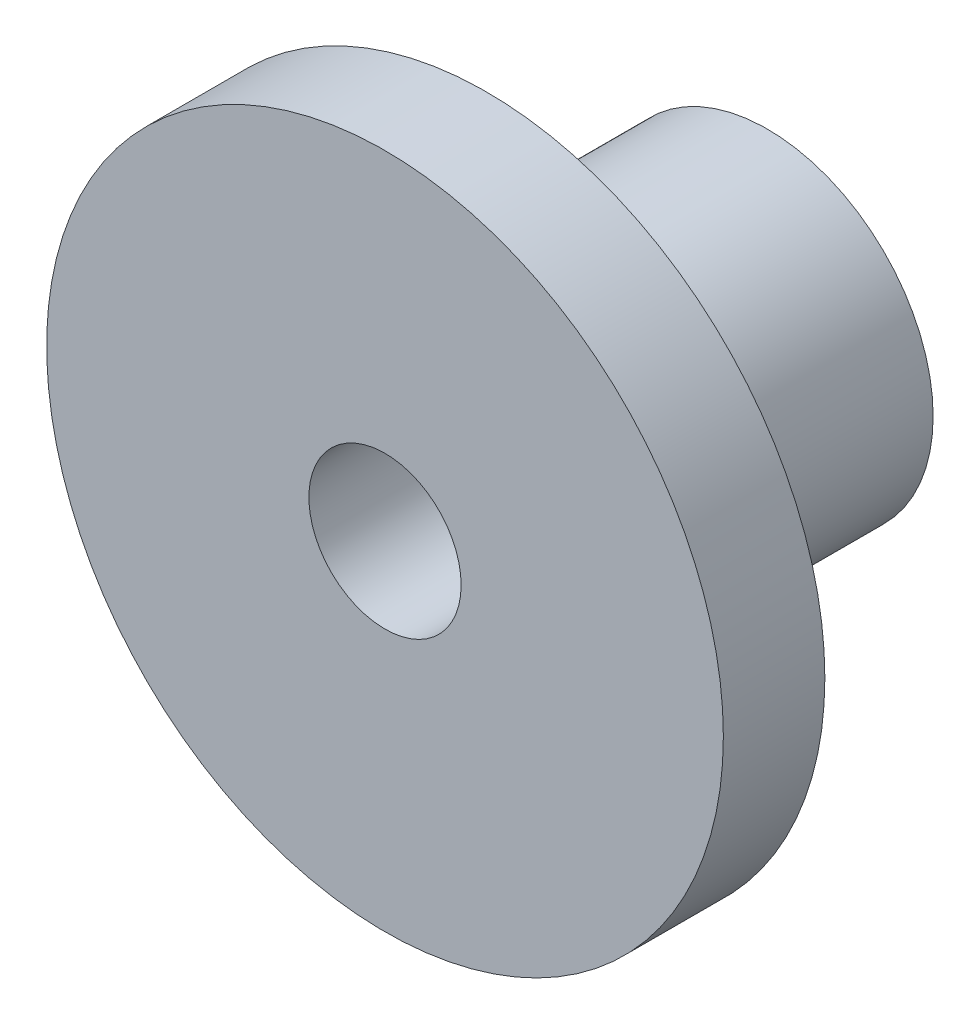
SolidWorks part; units mm, degrees
ref_plane "Front Plane" through (0, 0, 0) normal (0, 0, 1) x (1, 0, 0)
ref_plane "Top Plane" through (0, 0, 0) normal (0, 1, 0) x (1, 0, 0)
ref_plane "Right Plane" through (0, 0, 0) normal (1, 0, 0) x (0, 0, -1)
sketch "Sketch1" plane through (0, 0, 0) normal (0, 0, 1) x (1, 0, 0)
  circle A0 centre (0, 0) radius 4.9
  circle A1 centre (0, 0) radius 2.25
  dimension "D1" = 9.8
  dimension "D2" = 4.5
extrude "Boss-Extrude1" add sketch "Sketch1" along normal mid plane 8.3
sketch "Sketch2" plane through (0, 0, 4.15) normal (0, 0, 1) x (1, 0, 0)
  circle A0 centre (0, 0) radius 2.25
  circle A1 centre (0, 0) radius 10
  dimension "D1" = 20
extrude "Boss-Extrude2" add sketch "Sketch2" along normal blind 3
